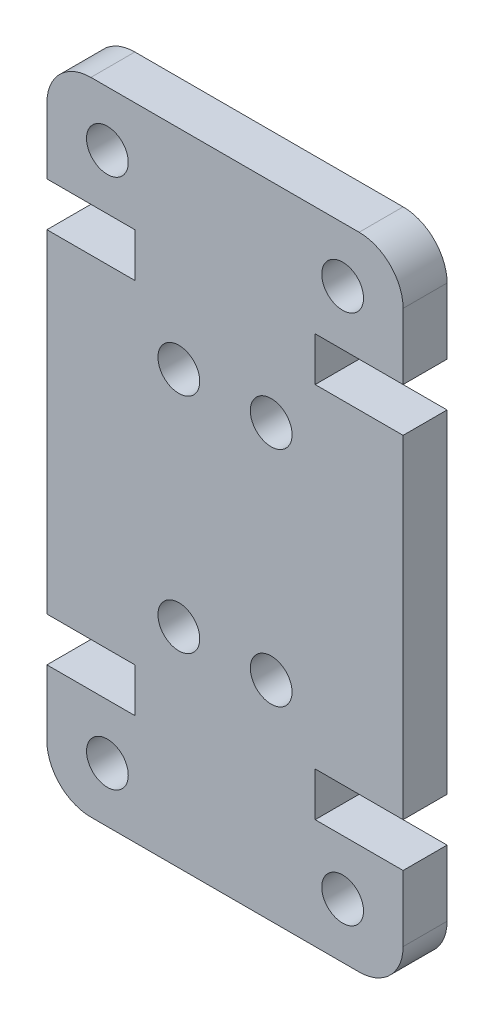
SolidWorks part; units mm, degrees
ref_plane "Front Plane" through (0, 0, 0) normal (0, 0, 1) x (1, 0, 0)
ref_plane "Top Plane" through (0, 0, 0) normal (0, 1, 0) x (1, 0, 0)
ref_plane "Right Plane" through (0, 0, 0) normal (1, 0, 0) x (0, 0, -1)
sketch "Sketch1" plane through (0, 0, 0) normal (0, 0, 1) x (1, 0, 0)
  line L0 (0, 22.14) -> (0, 7)
  line L1 (16.2, 2) -> (16.2, 5)
  line L2 (12.2, 5) -> (16.2, 5)
  line L3 (2, 0) -> (14.2, 0)
  line L4 (16.2, 7) -> (12.2, 7)
  line L5 (12.2, 7) -> (12.2, 5)
  line L6 (16.2, 22.14) -> (16.2, 7)
  line L7 (4, 7) -> (4, 5)
  line L8 (0, 27.14) -> (0, 24.14)
  line L9 (4, 24.14) -> (0, 24.14)
  line L10 (0, 7) -> (4, 7)
  line L11 (0, 22.14) -> (4, 22.14)
  line L12 (4, 5) -> (0, 5)
  line L13 (4, 22.14) -> (4, 24.14)
  line L14 (12.2, 22.14) -> (12.2, 24.14)
  line L15 (16.2, 22.14) -> (12.2, 22.14)
  line L16 (0, 2) -> (0, 5)
  line L17 (2, 29.14) -> (14.2, 29.14)
  line L18 (12.2, 24.14) -> (16.2, 24.14)
  line L19 (16.2, 27.14) -> (16.2, 24.14)
  line L20 (8.1, 29.14) -> (8.1, 0) construction
  line L21 (0, 14.57) -> (16.2, 14.57) construction
  circle A0 centre (13.45, 2.5) radius 0.95
  circle A1 centre (10.2, 9.5) radius 0.95
  arc A2 (16.2, 2) -> (14.2, 0) centre (14.2, 2) cw
  circle A3 centre (2.75, 26.64) radius 0.95
  circle A4 centre (6, 19.64) radius 0.95
  arc A5 (0, 2) -> (2, 0) centre (2, 2) ccw
  arc A6 (0, 27.14) -> (2, 29.14) centre (2, 27.14) cw
  circle A7 centre (6, 9.5) radius 0.95
  arc A8 (16.2, 27.14) -> (14.2, 29.14) centre (14.2, 27.14) ccw
  circle A9 centre (2.75, 2.5) radius 0.95
  circle A10 centre (10.2, 19.64) radius 0.95
  circle A11 centre (13.45, 26.64) radius 0.95
  point P15 (8.1, 14.57)
  dimension "D1" = 1.9
  dimension "D2" = 2
  dimension "D3" = 2.75
  dimension "D4" = 6
  dimension "D5" = 8.1
  dimension "D6" = 2.5
  dimension "D7" = 5
  dimension "D9" = 9.5
  dimension "D10" = 14.57
extrude "Boss-Extrude1" add sketch "Sketch1" along normal blind 2
equation "\"D5@Sketch1\"= \"fingerWidth@parametersSketch@prostheticParameters.SLDPRT\" / 2'PIP width"
equation "\"D10@Sketch1\"= ( \"HL@parametersSketch@prostheticParameters.SLDPRT\" * 0.244 - 4 - 12 ) / 2 'PIP length - Sil.Sht PIP - Sil. Sht MIP"
equation "\"D1@Sketch1\"= 1.5 + \"tol1@parametersSketch@prostheticParameters.SLDPRT\""
